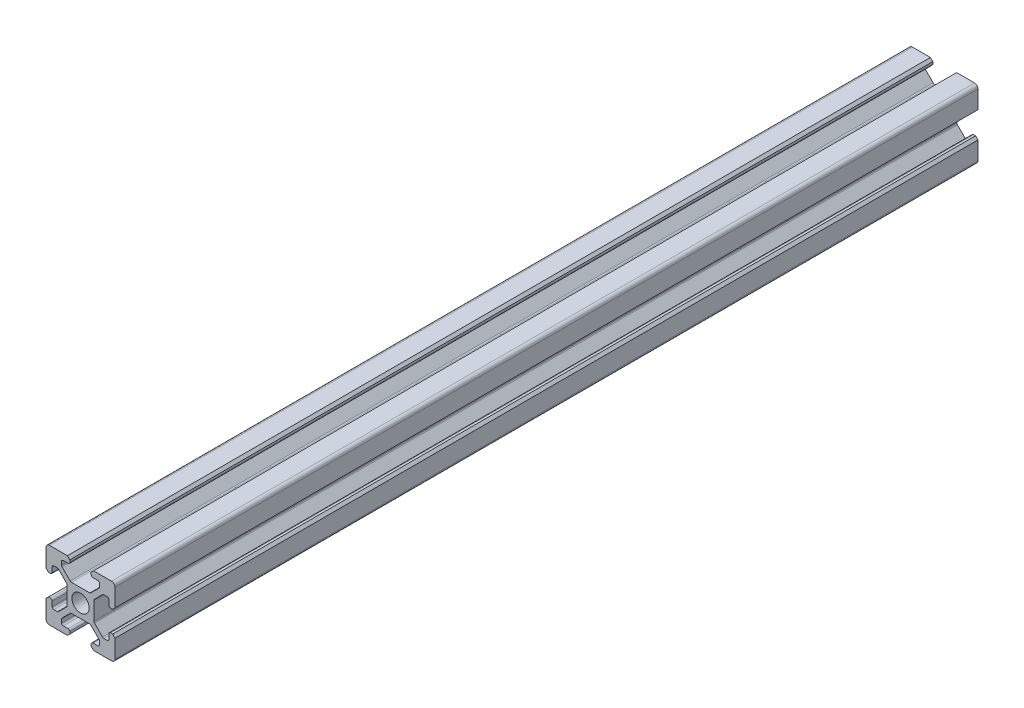
SolidWorks part; units mm, degrees
material "1060 Alloy"
ref_plane "Front Plane" through (0, 0, 0) normal (0, 0, 1) x (1, 0, 0)
ref_plane "Top Plane" through (0, 0, 0) normal (0, 1, 0) x (1, 0, 0)
ref_plane "Right Plane" through (0, 0, 0) normal (1, 0, 0) x (0, 0, -1)
sketch "Sketch1" plane through (0, 0, 0) normal (0, 0, 1) x (1, 0, 0)
  line L0 (3.9, -2.8393) -> (6.5607, -5.5)
  line L1 (-10, 10) -> (10, 10) construction
  line L2 (-10, 10) -> (-10, -10) construction
  line L3 (-10, -10) -> (10, -10) construction
  line L4 (10, 10) -> (10, -10) construction
  line L5 (-10, 10) -> (10, -10) construction
  line L6 (-10, -10) -> (10, 10) construction
  line L7 (-3.9, -3.9) -> (3.9, -3.9) construction
  line L8 (-3.9, -3.9) -> (-3.9, 3.9) construction
  line L9 (-3.9, 3.9) -> (3.9, 3.9) construction
  line L10 (3.9, -3.9) -> (3.9, 3.9) construction
  line L11 (-3.9, -3.9) -> (3.9, 3.9) construction
  line L12 (-3.9, 3.9) -> (3.9, -3.9) construction
  line L13 (-10, 10) -> (-5.5, 10) construction
  line L14 (-10, 10) -> (-10, 5.5) construction
  line L15 (-10, 5.5) -> (-5.5, 5.5) construction
  line L16 (-5.5, 10) -> (-5.5, 5.5) construction
  line L17 (10, 10) -> (5.5, 10) construction
  line L18 (10, 10) -> (10, 5.5) construction
  line L19 (10, 5.5) -> (5.5, 5.5) construction
  line L20 (5.5, 10) -> (5.5, 5.5) construction
  line L21 (-10, -10) -> (-5.5, -10) construction
  line L22 (-10, -10) -> (-10, -5.5) construction
  line L23 (-10, -5.5) -> (-5.5, -5.5) construction
  line L24 (-5.5, -10) -> (-5.5, -5.5) construction
  line L25 (10, -10) -> (5.5, -10) construction
  line L26 (10, -10) -> (10, -5.5) construction
  line L27 (10, -5.5) -> (5.5, -5.5) construction
  line L28 (5.5, -10) -> (5.5, -5.5) construction
  line L29 (2.8393, -3.9) -> (5.5, -6.5607)
  line L30 (-5.5, 6.5607) -> (-2.8393, 3.9)
  line L31 (-6.5607, 5.5) -> (-3.9, 2.8393)
  line L32 (5.5, 6.5607) -> (2.8393, 3.9)
  line L33 (6.5607, 5.5) -> (3.9, 2.8393)
  line L34 (-6.5607, -5.5) -> (-3.9, -2.8393)
  line L35 (-5.5, -6.5607) -> (-2.8393, -3.9)
  line L36 (-2.8393, 3.9) -> (2.8393, 3.9)
  line L37 (-3.9, 2.8393) -> (-3.9, -2.8393)
  line L38 (-2.8393, -3.9) -> (2.8393, -3.9)
  line L39 (3.9, -2.8393) -> (3.9, 2.8393)
  line L40 (5.5, 6.5607) -> (5.5, 8.2007)
  line L41 (5.5, 8.2007) -> (3.1, 8.2007)
  line L42 (3.1, 8.2007) -> (3.1, 9.3)
  line L43 (3.1, 9.3) -> (3.8, 10)
  line L44 (3.8, 10) -> (10, 10)
  line L45 (10, 10) -> (10, 3.8)
  line L46 (10, 3.8) -> (9.3, 3.1)
  line L47 (9.3, 3.1) -> (8.2007, 3.1)
  line L48 (8.2007, 3.1) -> (8.2007, 5.5)
  line L49 (8.2007, 5.5) -> (6.5607, 5.5)
  line L50 (3.1, -8.2007) -> (5.5, -8.2007)
  line L51 (3.1, -9.3) -> (3.1, -8.2007)
  line L52 (3.8, -10) -> (3.1, -9.3)
  line L53 (10, -10) -> (3.8, -10)
  line L54 (10, -3.8) -> (10, -10)
  line L55 (9.3, -3.1) -> (10, -3.8)
  line L56 (8.2007, -3.1) -> (9.3, -3.1)
  line L57 (8.2007, -5.5) -> (8.2007, -3.1)
  line L58 (6.5607, -5.5) -> (8.2007, -5.5)
  line L59 (5.5, -8.2007) -> (5.5, -6.5607)
  line L60 (-8.2007, -3.1) -> (-8.2007, -5.5)
  line L61 (-9.3, -3.1) -> (-8.2007, -3.1)
  line L62 (-10, -3.8) -> (-9.3, -3.1)
  line L63 (-10, -10) -> (-10, -3.8)
  line L64 (-3.8, -10) -> (-10, -10)
  line L65 (-3.1, -9.3) -> (-3.8, -10)
  line L66 (-3.1, -8.2007) -> (-3.1, -9.3)
  line L67 (-5.5, -8.2007) -> (-3.1, -8.2007)
  line L68 (-5.5, -6.5607) -> (-5.5, -8.2007)
  line L69 (-8.2007, -5.5) -> (-6.5607, -5.5)
  line L70 (-3.1, 8.2007) -> (-5.5, 8.2007)
  line L71 (-3.1, 9.3) -> (-3.1, 8.2007)
  line L72 (-3.8, 10) -> (-3.1, 9.3)
  line L73 (-10, 10) -> (-3.8, 10)
  line L74 (-10, 3.8) -> (-10, 10)
  line L75 (-9.3, 3.1) -> (-10, 3.8)
  line L76 (-8.2007, 3.1) -> (-9.3, 3.1)
  line L77 (-8.2007, 5.5) -> (-8.2007, 3.1)
  line L78 (-6.5607, 5.5) -> (-8.2007, 5.5)
  line L79 (-5.5, 8.2007) -> (-5.5, 6.5607)
  circle A0 centre (0, 0) radius 2.5
  point P83 (0, 0)
  dimension "D1" = 5
  dimension "D2" = 20
  dimension "D3" = 7.8
  dimension "D4" = 4.5
  dimension "D5" = 1.5
  dimension "D6" = 0.75
  dimension "D7" = 1.5
  dimension "D8" = 0.75
  dimension "D9" = 1.5
  dimension "D10" = 0.75
  dimension "D11" = 1.5
  dimension "D12" = 0.75
  dimension "D13" = 1.64
  dimension "D14" = 45
  dimension "D15" = 3.1
  dimension "D16" = 6.2
  dimension "D17" = 6.2
  dimension "D18" = 3.1
  dimension "D19" = 4
extrude "Boss-Extrude1" add sketch "Sketch1" along normal mid plane 250 contours L79 L70 L71 L72 L73 L74 L75 L76 L77 L78 L31 L37 L34 L69 L60 L61 L62 L63 L64 L65 L66 L67 L68 L35 L38 L29 L59 L50 L51 L52 L53 L54 L55 L56 L57 L58 L0 L39 L33 L49 L48 L47 L46 L45 L44 L43 L42 L41 L40 L32 L36
fillet "Fillet1" radius 0.5 8 edges at (2.8393, -3.9, 0) (-2.8393, -3.9, 0) (-3.9, 2.8393, 0) (-3.9, -2.8393, 0) (3.9, -2.8393, 0) (3.9, 2.8393, 0) (2.8393, 3.9, 0) (-2.8393, 3.9, 0)
fillet "Fillet2" radius 0.5 24 edges at (-8.2007, -3.1, 0) (-8.2007, -5.5, 0) (-6.5607, -5.5, 0) (-3.1, -8.2007, 0) (-5.5, -8.2007, 0) (-5.5, -6.5607, 0) (3.1, -8.2007, 0) (5.5, -6.5607, 0) (5.5, -8.2007, 0) (8.2007, -5.5, 0) (8.2007, -3.1, 0) (6.5607, -5.5, 0) (-8.2007, 3.1, 0) (-6.5607, 5.5, 0) (-8.2007, 5.5, 0) (6.5607, 5.5, 0) (8.2007, 5.5, 0) (8.2007, 3.1, 0) (5.5, 6.5607, 0) (5.5, 8.2007, 0) (3.1, 8.2007, 0) (-3.1, 8.2007, 0) (-5.5, 8.2007, 0) (-5.5, 6.5607, 0)
fillet "Fillet3" radius 1 4 edges at (-10, 10, 0) (-10, -10, 0) (10, 10, 0) (10, -10, 0)
sketch "Sketch2" plane through (0, 3.9, 0) normal (0, 1, 0) x (1, 0, 0)
  line L0 (0, 125) -> (0, 110.3536) construction
  line L1 (-2.6322, 125) -> (2.6322, 125) construction
  circle A0 centre (0, 117.4) radius 1.6
  dimension "D1" = 3.2
  dimension "D2" = 6
extrude "Cut-Extrude1" cut sketch "Sketch2" against normal through all
